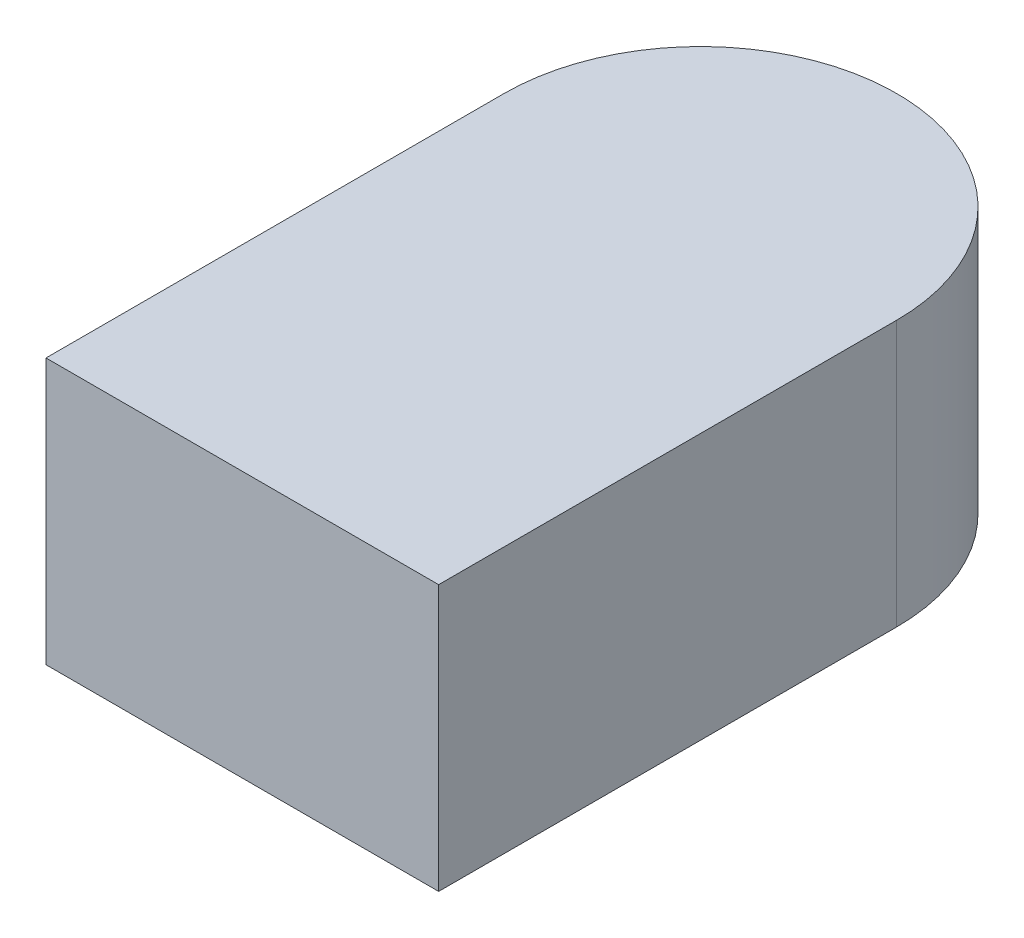
SolidWorks part; units mm, degrees
material "1060-H16"
ref_plane "Front Plane" through (0, 0, 0) normal (0, 0, 1) x (1, 0, 0)
ref_plane "Top Plane" through (0, 0, 0) normal (0, 1, 0) x (1, 0, 0)
ref_plane "Right Plane" through (0, 0, 0) normal (1, 0, 0) x (0, 0, -1)
sketch "Sketch1" plane through (0, 0, 0) normal (0, 1, 0) x (1, 0, 0)
  line L1 (-0.15, 0.175) -> (0.15, 0.175) construction
  line L2 (-0.15, 0.175) -> (-0.15, -0.175)
  line L3 (-0.15, -0.175) -> (0.15, -0.175)
  line L4 (0.15, 0.175) -> (0.15, -0.175)
  line L5 (-0.15, 0.175) -> (0.15, -0.175) construction
  line L6 (-0.15, -0.175) -> (0.15, 0.175) construction
  arc A0 (0.15, 0.175) -> (-0.15, 0.175) centre (0, 0.175) ccw
  point P0 (0, 0)
  point P7 (0, 0.325)
  dimension "D1" = 0.3
  dimension "D2" = 0.5
extrude "Boss-Extrude1" add sketch "Sketch1" along normal blind 0.203
